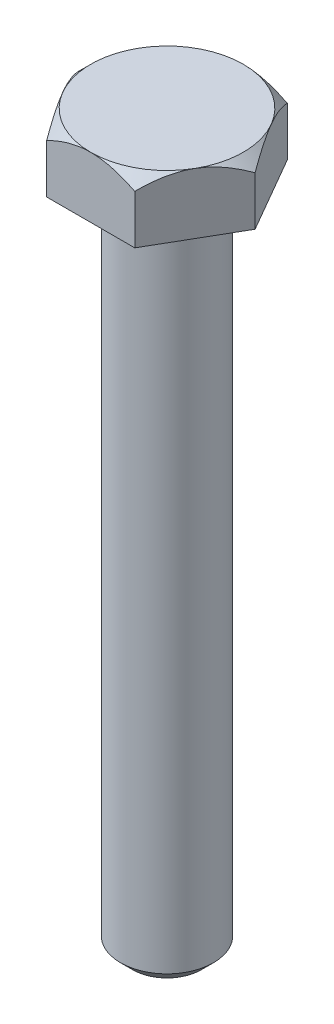
SolidWorks part; units mm, degrees
ref_plane "Спереди" through (0, 0, 0) normal (0, 0, 1) x (1, 0, 0)
ref_plane "Сверху" through (0, 0, 0) normal (0, 1, 0) x (1, 0, 0)
ref_plane "Справа" through (0, 0, 0) normal (1, 0, 0) x (0, 0, -1)
sketch "Эскиз6" plane through (0, 0, 0) normal (0, 1, 0) x (1, 0, 0)
  line L1 (7.25, 0) -> (3.625, 6.2787)
  line L2 (3.625, 6.2787) -> (-3.625, 6.2787)
  line L3 (-3.625, 6.2787) -> (-7.25, 0)
  line L4 (-7.25, 0) -> (-3.625, -6.2787)
  line L5 (-3.625, -6.2787) -> (3.625, -6.2787)
  line L6 (3.625, -6.2787) -> (7.25, 0)
  circle A0 centre (0, 0) radius 6.2787 construction
  dimension "D1" = 14.5
extrude "Бобышка-Вытянуть1" add sketch "Эскиз6" along normal blind 5
sketch "Эскиз8" plane through (0, 5, 0) normal (0, 1, 0) x (1, 0, 0)
  circle A0 centre (0, 0) radius 6.2787
extrude "Вырез-Вытянуть1" cut sketch "Эскиз8" against normal blind 1 draft 45 flip side to cut
sketch "Эскиз9" plane through (0, 0, 0) normal (0, -1, 0) x (1, 0, 0)
  circle A0 centre (0, 0) radius 3.825
  dimension "D1" = 7.65
extrude "bolt length" add sketch "Эскиз9" along normal blind 55
fillet "Скругление1" radius 1 1 edges at (0, 0, 3.825)
chamfer "Фаска1" distance 1 angle 45 1 edges at (0, -55, -3.825)
